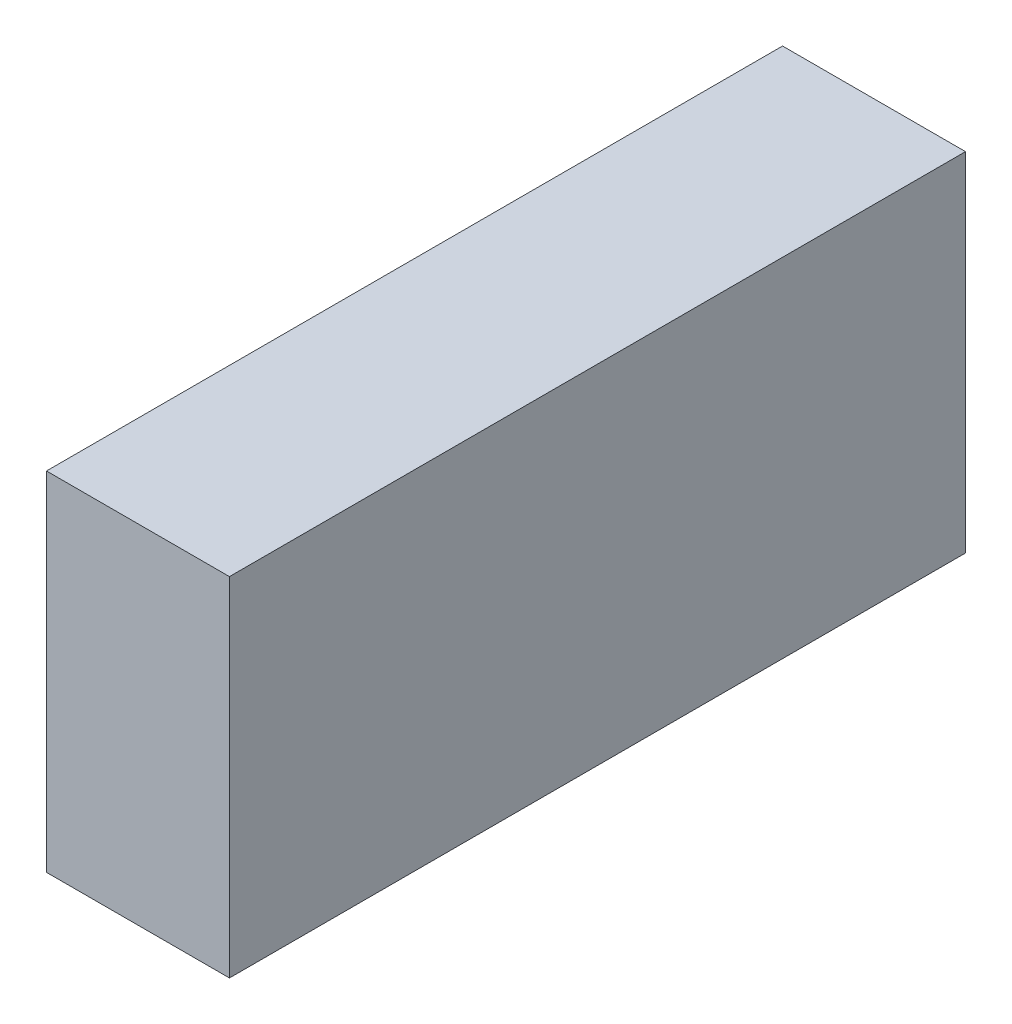
SolidWorks part; units mm, degrees
ref_plane "Front Plane" through (0, 0, 0) normal (0, 0, 1) x (1, 0, 0)
ref_plane "Top Plane" through (0, 0, 0) normal (0, 1, 0) x (1, 0, 0)
ref_plane "Right Plane" through (0, 0, 0) normal (1, 0, 0) x (0, 0, -1)
sketch "Sketch1" plane through (0, 0, 0) normal (0, 0, 1) x (1, 0, 0)
  line L1 (-7.8639, 15.3704) -> (5.1361, 15.3704)
  line L2 (-7.8639, 15.3704) -> (-7.8639, -9.3296)
  line L3 (-7.8639, -9.3296) -> (5.1361, -9.3296)
  line L4 (5.1361, 15.3704) -> (5.1361, -9.3296)
  dimension "D1" = 13
  dimension "D2" = 24.7
extrude "Extrude1" add sketch "Sketch1" along normal blind 52.3
